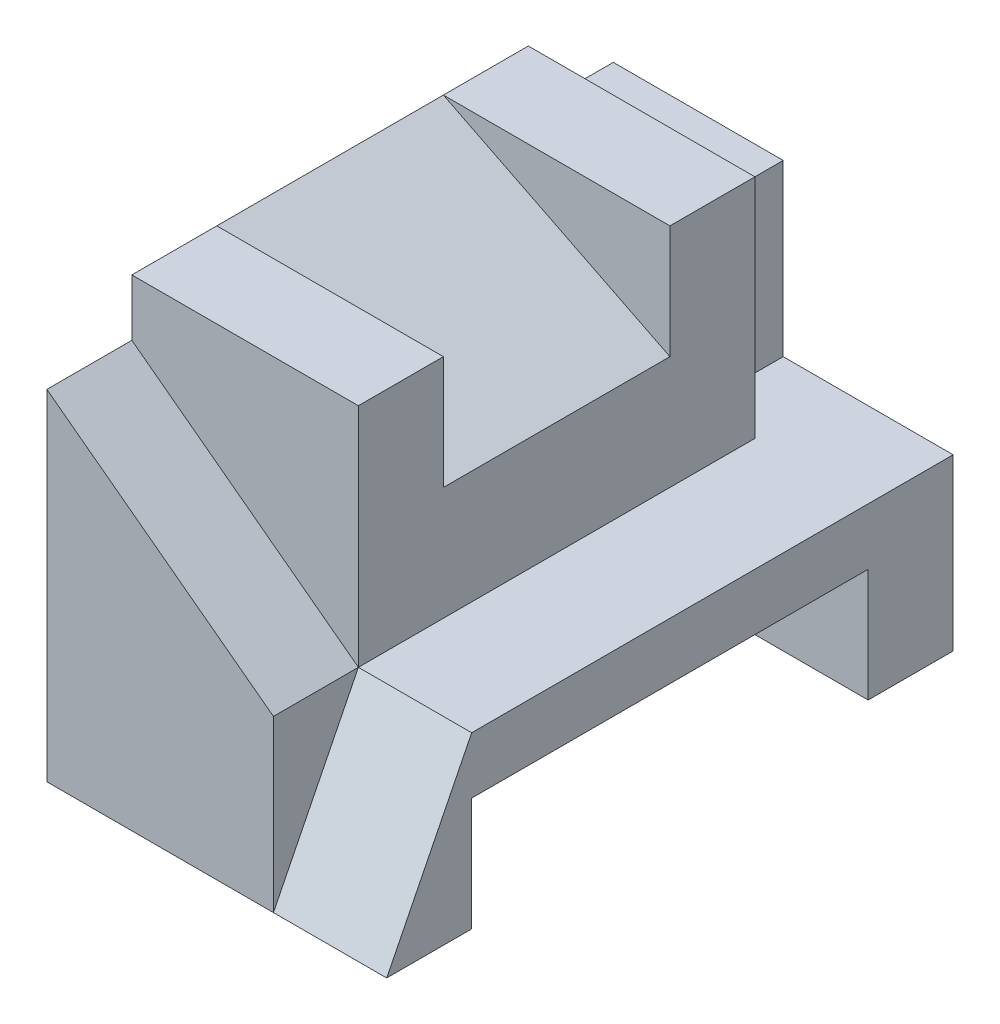
SolidWorks part; units mm, degrees
ref_plane "Alzado" through (0, 0, 0) normal (0, 0, 1) x (1, 0, 0)
ref_plane "Planta" through (0, 0, 0) normal (0, 1, 0) x (1, 0, 0)
ref_plane "Vista lateral" through (0, 0, 0) normal (1, 0, 0) x (0, 0, -1)
sketch "Croquis2" plane through (0, 0, 0) normal (1, 0, 0) x (0, 0, -1)
  line L0 (0, 0) -> (0, -3)
  line L1 (0, -3) -> (1.5, -3)
  line L2 (1.5, -3) -> (1.5, -1)
  line L3 (1.5, -1) -> (8.5, -1)
  line L4 (8.5, -1) -> (8.5, -3)
  line L5 (8.5, -3) -> (10, -3)
  line L6 (10, -3) -> (10, 0)
  line L7 (10, 0) -> (0, 0)
  dimension "D1" = 7
  dimension "D2" = 3
  dimension "D3" = 1.5
  dimension "D4" = 1.5
  dimension "D5" = 2
  dimension "D6" = 3
extrude "Saliente-Extruir2" add sketch "Croquis2" along normal blind 6
sketch "Croquis5" plane through (6, 0, 0) normal (1, 0, 0) x (0, 0, -1)
  line L0 (0, -3) -> (1.5, 0)
  line L1 (10, 0) -> (0, 0) construction
  line L2 (1.5, 0) -> (0, 0)
  line L3 (0, 0) -> (0, -3)
extrude "Cortar-Extruir2" cut sketch "Croquis5" against normal blind 2
sketch "Croquis6" plane through (0, 0, 0) normal (0, 1, 0) x (1, 0, 0)
  line L0 (4, 0) -> (4, 8)
  line L1 (4, 8) -> (0, 8)
  line L2 (0, 10) -> (0, 0) construction
  line L3 (0, 8) -> (0, 0)
  line L4 (0, 0) -> (4, 0)
extrude "Saliente-Extruir3" add sketch "Croquis6" along normal blind 4
sketch "Croquis7" plane through (0, 0, 0) normal (0, 0, 1) x (1, 0, 0)
  line L2 (0, 4) -> (0, -3) construction
  line L3 (0, 3) -> (4, 0)
  line L7 (0, 3) -> (0, 4)
  line L8 (0, 4) -> (4, 4)
  line L9 (4, 4) -> (4, 0)
extrude "Cortar-Extruir3" cut sketch "Croquis7" against normal blind 1.5
sketch "Croquis9" plane through (4, 0, 0) normal (1, 0, 0) x (0, 0, -1)
  line L0 (1.5, 4) -> (3, 4)
  line L1 (1.5, 4) -> (8, 4) construction
  line L2 (3, 4) -> (3, 2)
  line L3 (3, 2) -> (7, 2)
  line L4 (7, 2) -> (7, 4)
  line L5 (3, 4) -> (7, 4)
  line M5 (8, 4) -> (1.5, 4)
  dimension "D1" = 2
extrude "Cortar-Extruir4" cut sketch "Croquis9" against normal blind 5 contours L3 L4 L2 M5
sketch "Croquis10" plane through (4, 0, 0) normal (1, 0, 0) x (0, 0, -1)
  line L0 (7, 4) -> (8.5, 4)
  line L1 (8.5, 4) -> (8.5, 0)
  line L2 (10, 0) -> (1.5, 0) construction
  line L3 (8.5, 0) -> (7, 0)
  line L4 (1.5, 0) -> (8, 0) construction
  line L5 (7, 0) -> (7, 4)
extrude "Saliente-Extruir4" add sketch "Croquis10" against normal blind 4
sketch "Croquis12" plane through (0, 0, -7) normal (0, 0, 1) x (1, 0, 0)
  line L0 (0, 4) -> (4, 2)
  line L1 (4, 2) -> (0, 2)
  line L2 (0, 2) -> (0, 4)
extrude "Saliente-Extruir5" add sketch "Croquis12" along normal blind 4
sketch "Croquis13" plane through (0, 0, -8.5) normal (0, 0, -1) x (-1, 0, 0)
  line L0 (0, 4) -> (0, 3) construction
  line L1 (0, 0) -> (0, 4) construction
  line L2 (0, 0) -> (-4, 0) construction
  line L3 (0, 3) -> (-3, 3)
  line L4 (0, 3) -> (0, 0)
  line L5 (0, 0) -> (-3, 0)
  line L6 (-3, 3) -> (-3, 0)
  dimension "D1" = 3
  dimension "D2" = 3
extrude "Saliente-Extruir6" add sketch "Croquis13" along normal blind 1.5
